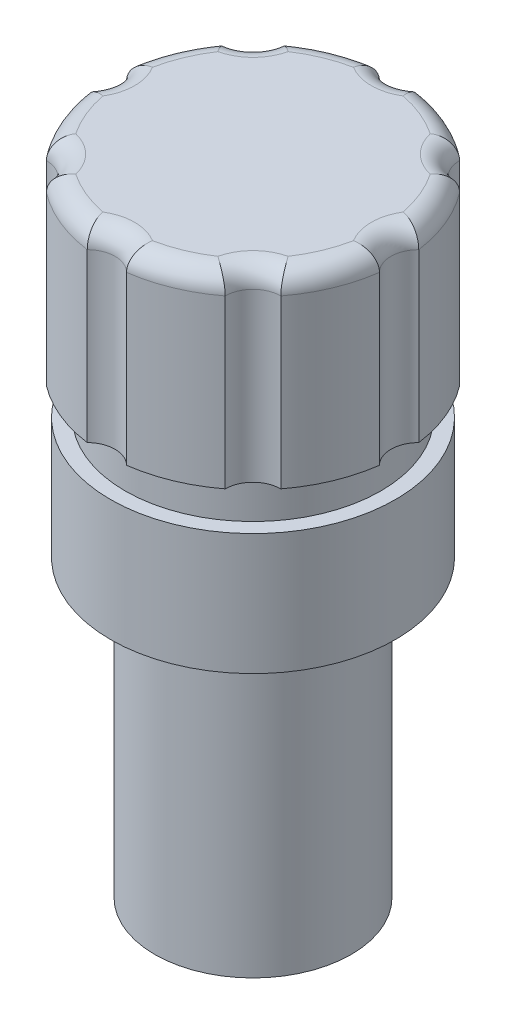
SolidWorks part; units mm, degrees
ref_plane "Front Plane" through (0, 0, 0) normal (0, 0, 1) x (1, 0, 0)
ref_plane "Top Plane" through (0, 0, 0) normal (0, 1, 0) x (1, 0, 0)
ref_plane "Right Plane" through (0, 0, 0) normal (1, 0, 0) x (0, 0, -1)
sketch "Sketch1" plane through (0, 0, 0) normal (0, 1, 0) x (1, 0, 0)
  circle A0 centre (0, 0) radius 10
  dimension "D1" = 20
extrude "Boss-Extrude1" add sketch "Sketch1" along normal blind 30
sketch "Sketch2" plane through (0, 30, 0) normal (0, 1, 0) x (1, 0, 0)
  circle A0 centre (0, 0) radius 14.5
  dimension "D1" = 29
extrude "Boss-Extrude2" add sketch "Sketch2" along normal blind 12.34
sketch "Sketch3" plane through (0, 42.34, 0) normal (0, 1, 0) x (1, 0, 0)
  circle A0 centre (0, 0) radius 13
extrude "Boss-Extrude3" add sketch "Sketch3" along normal blind 4.2
sketch "Sketch4" plane through (0, 46.54, 0) normal (0, 1, 0) x (1, 0, 0)
  circle A0 centre (0, 0) radius 15
  dimension "D1" = 30
extrude "Boss-Extrude4" add sketch "Sketch4" along normal blind 19
sketch "Sketch5" plane through (0, 65.54, 0) normal (0, 1, 0) x (1, 0, 0)
  line L0 (0, 0) -> (0, 15) construction
  line L1 (2, 0) -> (2, 15) construction
  line L2 (-2, 0) -> (-2, 15) construction
  circle A0 centre (0, 0) radius 15 construction
  arc A1 (-14.8661, 2.0001) -> (-14.8661, -2) centre (0, 0) ccw
  arc A2 (-2, 14.8661) -> (2.0001, 14.8661) centre (0.0001, 16.866) ccw
  arc A3 (9.0977, 11.9261) -> (11.9262, 9.0976) centre (11.9261, 11.926) ccw
  arc A4 (14.8661, 2) -> (14.8661, -2.0001) centre (16.866, -0.0001) ccw
  arc A5 (11.9261, -9.0977) -> (9.0976, -11.9262) centre (11.926, -11.9261) ccw
  arc A6 (2, -14.8661) -> (-2.0001, -14.8661) centre (-0.0001, -16.866) ccw
  arc A7 (-9.0977, -11.9261) -> (-11.9262, -9.0976) centre (-11.9261, -11.926) ccw
  arc A8 (-14.8661, -2) -> (-14.8661, 2.0001) centre (-16.866, 0.0001) ccw
  arc A9 (-11.9261, 9.0977) -> (-9.0976, 11.9262) centre (-11.926, 11.9261) ccw
  arc A10 (-9.0976, 11.9262) -> (-11.9261, 9.0977) centre (0, 0) ccw
  arc A11 (2.0001, 14.8661) -> (-2, 14.8661) centre (0, 0) ccw
  arc A12 (11.9262, 9.0976) -> (9.0977, 11.9261) centre (0, 0) ccw
  arc A13 (14.8661, -2.0001) -> (14.8661, 2) centre (0, 0) ccw
  arc A14 (9.0976, -11.9262) -> (11.9261, -9.0977) centre (0, 0) ccw
  arc A15 (-2.0001, -14.8661) -> (2, -14.8661) centre (0, 0) ccw
  arc A16 (-11.9262, -9.0976) -> (-9.0977, -11.9261) centre (0, 0) ccw
  point P36 (0, 0)
  dimension "D3" = 2.8284
  dimension "D1" = 2
  dimension "D2" = 2
  dimension "D4" = 8
extrude "Cut-Extrude1" cut sketch "Sketch5" against normal blind 19
fillet "Fillet2" radius 2 16 edges at (-0.0001, 65.54, 14.0376) (-5.7403, 65.54, 13.8582) (-9.9261, 65.54, 9.926) (-13.8582, 65.54, 5.7402) (-14.0376, 65.54, -0.0001) (-13.8582, 65.54, -5.7403) (-9.926, 65.54, -9.9261) (-5.7402, 65.54, -13.8582) (0.0001, 65.54, -14.0376) (5.7403, 65.54, -13.8582) (9.9261, 65.54, -9.926) (13.8582, 65.54, -5.7402) (14.0376, 65.54, 0.0001) (13.8582, 65.54, 5.7403) (9.926, 65.54, 9.9261) (5.7402, 65.54, 13.8582)
